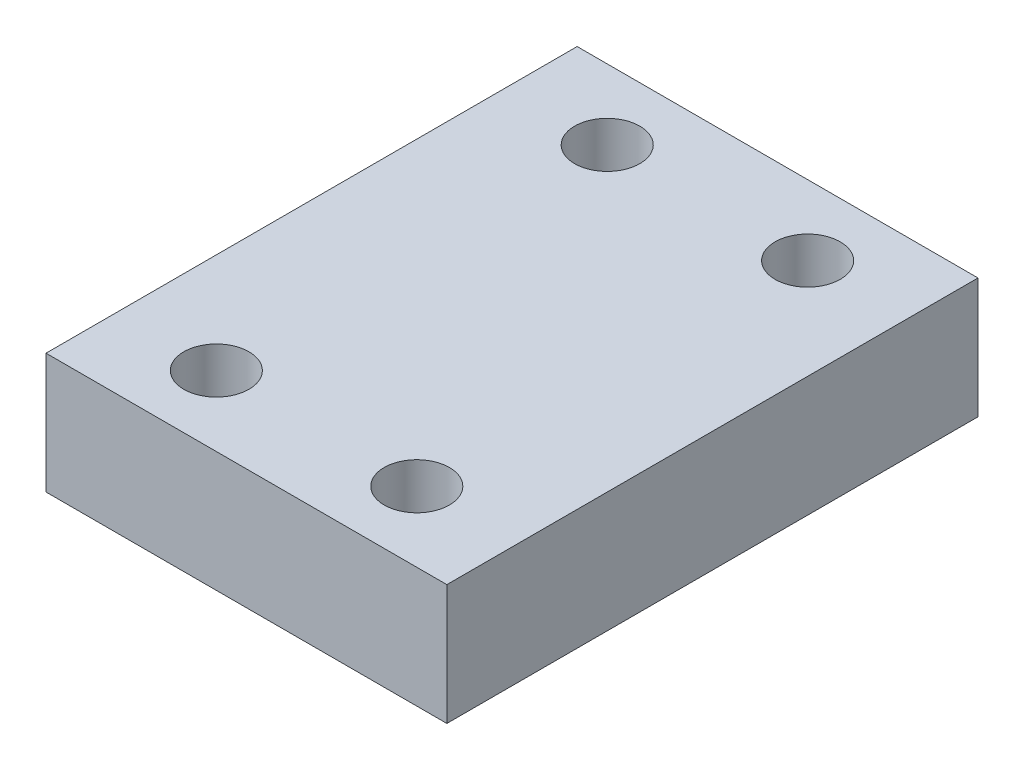
SolidWorks part; units mm, degrees
ref_plane "Front Plane" through (0, 0, 0) normal (0, 0, 1) x (1, 0, 0)
ref_plane "Top Plane" through (0, 0, 0) normal (0, 1, 0) x (1, 0, 0)
ref_plane "Right Plane" through (0, 0, 0) normal (1, 0, 0) x (0, 0, -1)
sketch "Sketch1" plane through (0, 0, 0) normal (0, 1, 0) x (1, 0, 0)
  line L0 (13.8021, -16.7414) -> (-19.1979, -16.7414) construction
  line L6 (-17.5215, -33.2414) -> (22.4785, -33.2414)
  line L7 (13.8021, 3.2586) -> (-8.845, 3.2586) construction
  line L8 (13.8021, 3.2586) -> (13.8021, -16.7414) construction
  line L9 (13.8021, -16.7414) -> (-8.845, -16.7414) construction
  line L10 (-8.845, 3.2586) -> (-8.845, -16.7414) construction
  line L11 (-8.845, 3.2586) -> (13.8021, -16.7414) construction
  line L12 (-8.845, -16.7414) -> (13.8021, 3.2586) construction
  line L13 (-17.5215, -33.2414) -> (-17.5215, 19.7586)
  line L14 (-17.5215, 19.7586) -> (22.4785, 19.7586)
  line L15 (22.4785, -33.2414) -> (22.4785, 19.7586)
  line L16 (-17.5215, -33.2414) -> (22.4785, 19.7586) construction
  line L17 (-17.5215, 19.7586) -> (22.4785, -33.2414) construction
  point P0 (0, 0)
  point P1 (2.4785, -6.7414)
  dimension "D1" = 53
  dimension "D2" = 40
extrude "Boss-Extrude1" add sketch "Sketch1" along normal blind 12
sketch "Sketch2" plane through (0, 0, 0) normal (0, -1, 0) x (1, 0, 0)
  line L0 (2.4785, -19.7586) -> (2.4785, 33.2414) construction
  line L1 (22.4785, -19.7586) -> (-17.5215, -19.7586) construction
  line L2 (-17.5215, 33.2414) -> (22.4785, 33.2414) construction
  circle A0 centre (2.4785, 6.7414) radius 8
  dimension "D1" = 16
extrude "Cut-Extrude1" cut sketch "Sketch2" against normal blind 3.5
sketch "Sketch4" plane through (0, 3.5, 0) normal (0, -1, 0) x (1, 0, 0)
  circle A0 centre (2.4785, 6.7414) radius 4.25
  dimension "D1" = 8.5
extrude "Cut-Extrude2" cut sketch "Sketch4" against normal blind 1.5
sketch "Sketch5" plane through (0, 12, 0) normal (0, 1, 0) x (1, 0, 0)
  line L0 (-17.5215, -26.2414) -> (22.4785, -26.2414) construction
  line L1 (-17.5215, 19.7586) -> (-17.5215, -33.2414) construction
  line L2 (22.4785, -33.2414) -> (22.4785, 19.7586) construction
  line L3 (-17.5215, 12.7586) -> (22.4785, 12.7586) construction
  line L4 (-17.5215, -33.2414) -> (22.4785, -33.2414) construction
  line L5 (22.4785, 19.7586) -> (-17.5215, 19.7586) construction
  circle A0 centre (-7.5215, -26.2414) radius 3.25
  circle A1 centre (12.4785, -26.2414) radius 3.25
  circle A2 centre (-7.5215, 12.7586) radius 3.25
  circle A3 centre (12.4785, 12.7586) radius 3.25
  dimension "D3" = 6.5
  dimension "D4" = 6.5
  dimension "D5" = 6.5
  dimension "D6" = 6.5
  dimension "D1" = 7
  dimension "D2" = 7
  dimension "D7" = 10
  dimension "D8" = 10
  dimension "D9" = 10
  dimension "D10" = 10
extrude "Cut-Extrude3" cut sketch "Sketch5" against normal up to next
sketch "Sketch6" plane through (0, 0, 0) normal (0, 1, 0) x (1, 0, 0)
  line L5 (22.4785, -33.2414) -> (22.4785, 19.7586)
  line L6 (-17.5215, -33.2414) -> (22.4785, -33.2414)
  line L7 (-17.5215, 19.7586) -> (-17.5215, -33.2414)
  line L8 (22.4785, 19.7586) -> (-17.5215, 19.7586)
  line L9 (22.4785, -33.2414) -> (22.4785, 19.7586)
  line L10 (-17.5215, -33.2414) -> (22.4785, -33.2414)
  line L11 (-17.5215, 19.7586) -> (-17.5215, -33.2414)
  line L12 (22.4785, 19.7586) -> (-17.5215, 19.7586)
  circle A0 centre (2.4785, -6.7414) radius 8 construction
  circle A1 centre (12.4785, 12.7586) radius 3.25 construction
  circle A2 centre (-7.5215, 12.7586) radius 3.25 construction
  circle A3 centre (-7.5215, -26.2414) radius 3.25 construction
  circle A4 centre (12.4785, -26.2414) radius 3.25 construction
  circle A5 centre (2.4785, -6.7414) radius 4.25 construction
  circle A6 centre (2.4785, -6.7414) radius 4.25
  circle A7 centre (12.4785, -26.2414) radius 3.25
  circle A8 centre (-7.5215, -26.2414) radius 3.25
  circle A9 centre (-7.5215, 12.7586) radius 3.25
  circle A10 centre (12.4785, 12.7586) radius 3.25
  circle A11 centre (2.4785, -6.7414) radius 8
  dimension "D1" = 0
